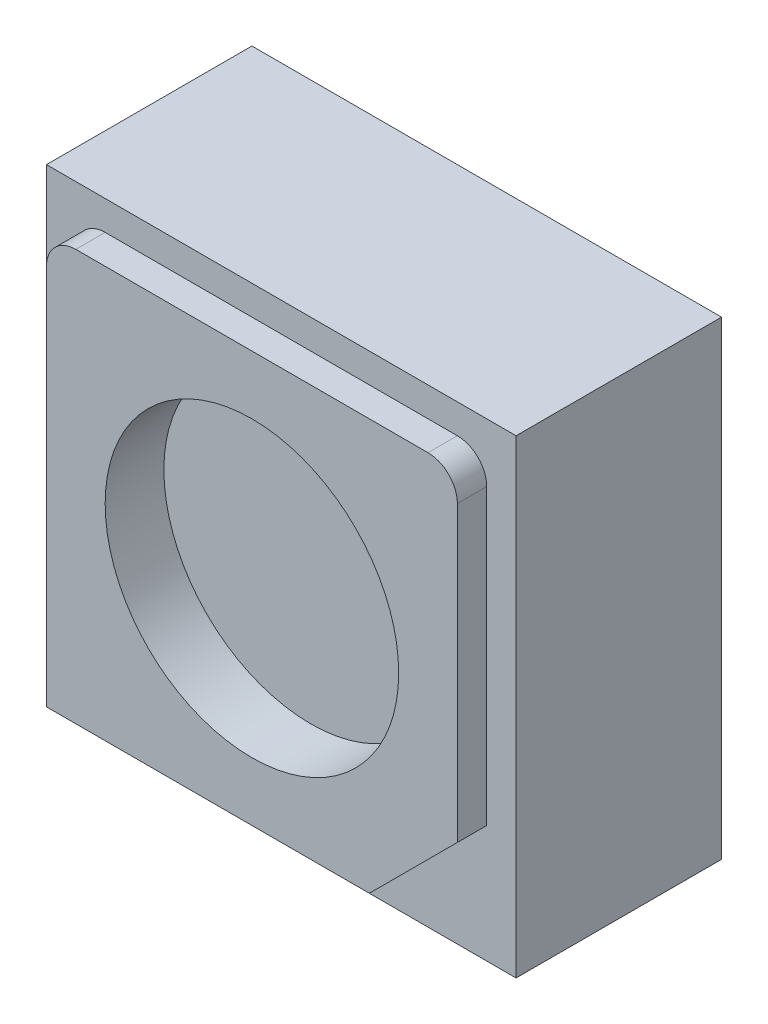
SolidWorks part; units mm, degrees
ref_plane "Front Plane" through (0, 0, 0) normal (0, 0, 1) x (1, 0, 0)
ref_plane "Top Plane" through (0, 0, 0) normal (0, 1, 0) x (1, 0, 0)
ref_plane "Right Plane" through (0, 0, 0) normal (1, 0, 0) x (0, 0, -1)
sketch "Sketch1" plane through (0, 0, 0) normal (0, 0, 1) x (1, 0, 0)
  line L1 (0, 0) -> (80, 0)
  line L2 (0, 0) -> (0, 80)
  line L3 (0, 80) -> (80, 80)
  line L4 (80, 0) -> (80, 80)
  dimension "D1" = 80
extrude "Boss-Extrude1" add sketch "Sketch1" along normal blind 35
sketch "Sketch2" plane through (0, 0, 0) normal (0, 0, 1) x (1, 0, 0)
  line L0 (60, 5) -> (75, 20)
  line L1 (5, 5) -> (60, 5)
  line L2 (5, 5) -> (5, 70)
  line L3 (10, 75) -> (70, 75)
  line L4 (75, 20) -> (75, 70)
  line L5 (80, 80) -> (0, 80) construction
  line L6 (0, 80) -> (0, 0) construction
  arc A0 (70, 75) -> (75, 70) centre (70, 70) cw
  arc A1 (5, 70) -> (10, 75) centre (10, 70) cw
  point P3 (75, 5)
  dimension "D1" = 5
  dimension "D2" = 5
  dimension "D3" = 5
  dimension "D5" = 70
  dimension "D6" = 70
extrude "Boss-Extrude2" add sketch "Sketch2" along normal blind 5 from offset 35
sketch "Sketch3" plane through (0, 0, 0) normal (0, 0, 1) x (1, 0, 0)
  circle A0 centre (40, 40) radius 25
extrude "Cut-Extrude1" cut sketch "Sketch3" against normal blind 10 from offset 40
